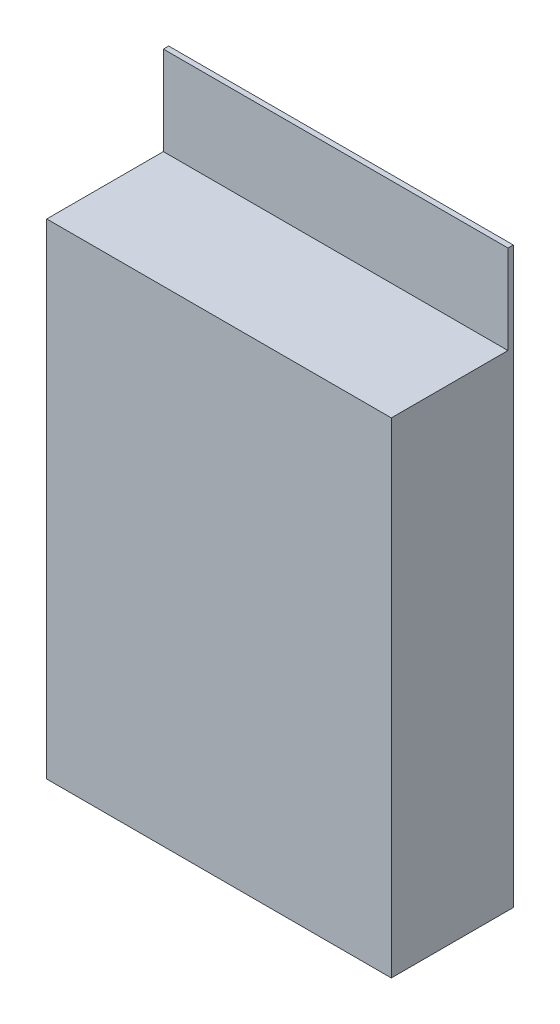
SolidWorks part; units mm, degrees
ref_plane "Front Plane" through (0, 0, 0) normal (0, 0, 1) x (1, 0, 0)
ref_plane "Top Plane" through (0, 0, 0) normal (0, 1, 0) x (1, 0, 0)
ref_plane "Right Plane" through (0, 0, 0) normal (1, 0, 0) x (0, 0, -1)
sketch "Sketch1" plane through (0, 0, 0) normal (0, 0, 1) x (1, 0, 0)
  line L1 (-33.02, 46.482) -> (33.02, 46.482)
  line L2 (-33.02, 46.482) -> (-33.02, -46.482)
  line L3 (-33.02, -46.482) -> (33.02, -46.482)
  line L4 (33.02, 46.482) -> (33.02, -46.482)
  line L5 (-33.02, 46.482) -> (33.02, -46.482) construction
  line L6 (-33.02, -46.482) -> (33.02, 46.482) construction
  point P0 (0, 0)
  dimension "D1" = 66.04
  dimension "D2" = 92.964
extrude "Boss-Extrude1" add sketch "Sketch1" along normal blind 23.368
sketch "Sketch3" plane through (0, 46.482, 0) normal (0, 1, 0) x (1, 0, 0)
  line L0 (33.02, -23.368) -> (33.02, 0) construction
  line L1 (-33.02, 0) -> (33.02, 0)
  line L2 (-33.02, 0) -> (-33.02, -1.016)
  line L3 (-33.02, -1.016) -> (33.02, -1.016)
  line L4 (33.02, 0) -> (33.02, -1.016)
  dimension "D1" = 1.016
extrude "Boss-Extrude2" add sketch "Sketch3" along normal blind 17.018
